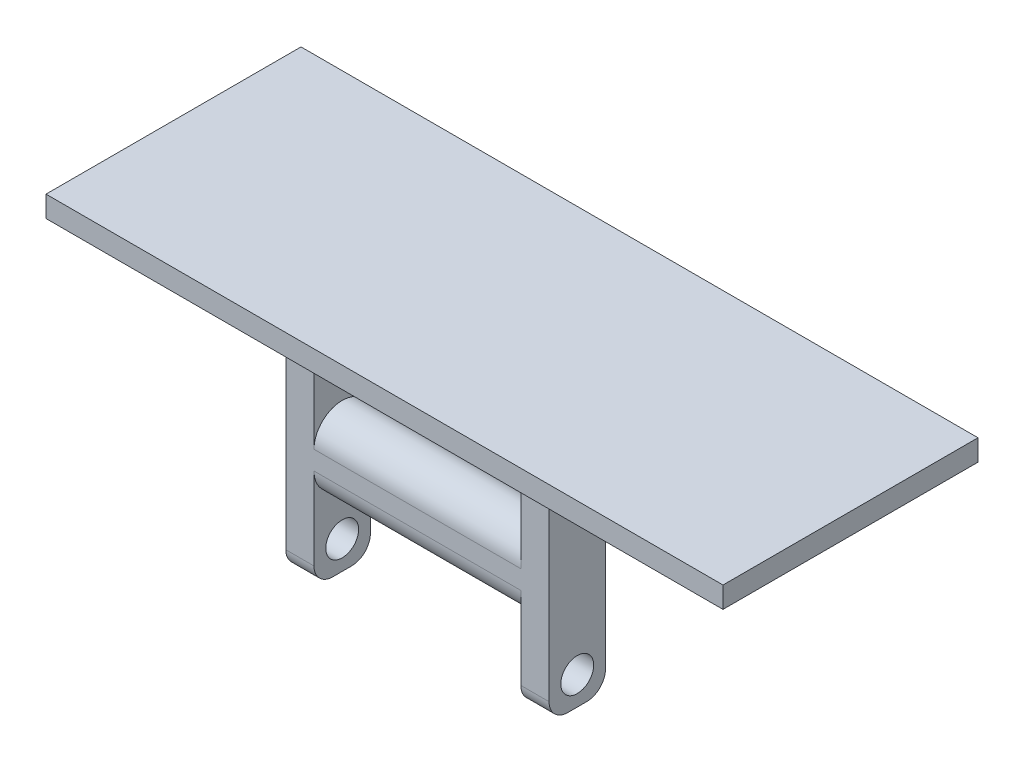
SolidWorks part; units mm, degrees
ref_plane "Alzado" through (0, 0, 0) normal (0, 0, 1) x (1, 0, 0)
ref_plane "Planta" through (0, 0, 0) normal (0, 1, 0) x (1, 0, 0)
ref_plane "Vista lateral" through (0, 0, 0) normal (1, 0, 0) x (0, 0, -1)
sketch "Croquis2" plane through (0, 0, 0) normal (1, 0, 0) x (0, 0, -1)
  line L0 (0, -1) -> (0, 1) construction
  line L1 (-3, -1) -> (-3, 1)
  line L2 (3, -1) -> (3, 1)
  arc A0 (-3, -1) -> (3, -1) centre (0, -1) ccw
  arc A1 (3, 1) -> (-3, 1) centre (0, 1) ccw
  point P2 (0, 0)
  dimension "D2" = 3
  dimension "D1" = 2
extrude "Saliente-Extruir1" add sketch "Croquis2" along normal blind 14
sketch "Croquis3" plane through (14, 0, 0) normal (1, 0, 0) x (0, 0, -1)
  line L0 (0, 8.75) -> (0, -8.75) construction
  line L1 (-3, 11.75) -> (3, 11.75)
  line L2 (-3, 11.75) -> (-3, -11.75)
  line L3 (-3, -11.75) -> (3, -11.75)
  line L4 (3, 11.75) -> (3, -11.75)
  line L5 (-3, 11.75) -> (3, -11.75) construction
  line L6 (-3, -11.75) -> (3, 11.75) construction
  circle A0 centre (0, 8.75) radius 1.75
  circle A1 centre (0, -8.75) radius 1.75
  point P0 (0, 0)
  point P9 (0, 0)
  dimension "D2" = 3.5
  dimension "D3" = 6
  dimension "D4" = 23.5
  dimension "D1" = 3.5
  dimension "D5" = 17.5
extrude "Saliente-Extruir2" add sketch "Croquis3" against normal blind 3
fillet "Redondeo1" radius 2 2 edges at (12.5, -11.75, 3) (12.5, -11.75, -3)
mirror "Simetría1" about plane through (0, 0, 0) normal (1, 0, 0) of "Saliente-Extruir2", "Saliente-Extruir1", "Redondeo1"
sketch "Croquis6" plane through (0, 11.75, 0) normal (0, 1, 0) x (1, 0, 0)
  line L5 (-36, -6.5) -> (36, -6.5)
  line L6 (-36, -6.5) -> (-36, 20.6199)
  line L7 (-36, 20.6199) -> (36, 20.6199)
  line L8 (36, -6.5) -> (36, 20.6199)
  point P0 (0, 0)
  point P6 (0, 0)
  point P7 (0, 0)
extrude "Saliente-Extruir5" add sketch "Croquis6" along normal blind 2 and the other way up to surface (0.25 mm away)
